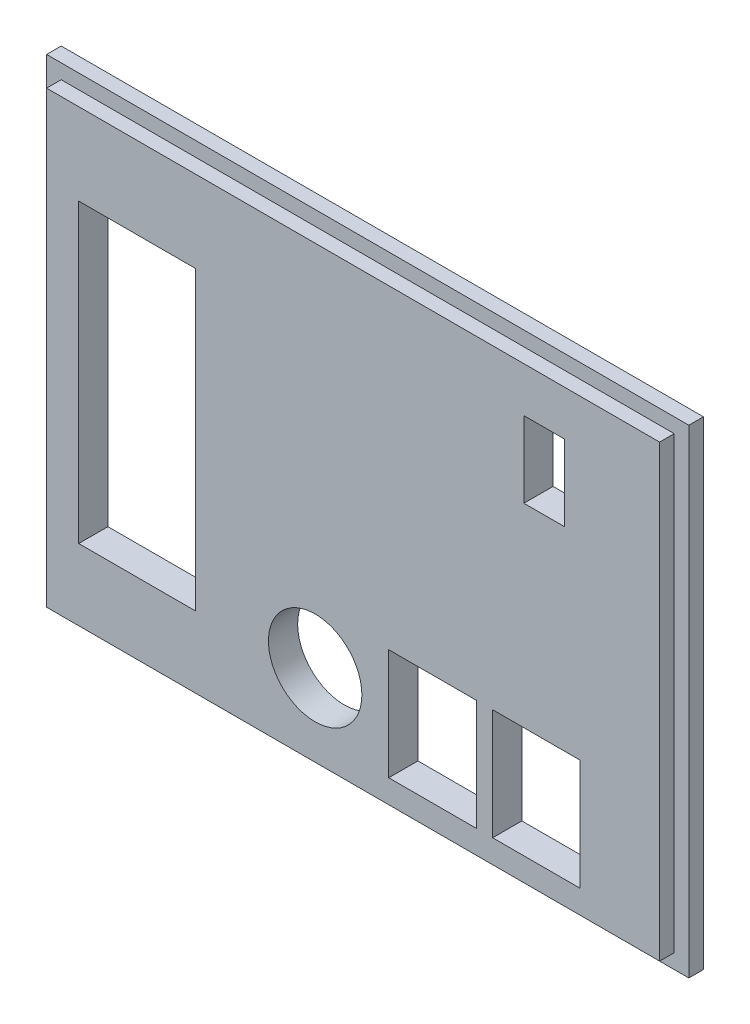
SolidWorks part; units mm, degrees
ref_plane "Front" through (0, 0, 0) normal (0, 0, 1) x (1, 0, 0)
ref_plane "Top" through (0, 0, 0) normal (0, 1, 0) x (1, 0, 0)
ref_plane "Right" through (0, 0, 0) normal (1, 0, 0) x (0, 0, -1)
sketch "Sketch2" plane through (0, 0, 0) normal (0, 0, 1) x (1, 0, 0)
  line L1 (55, 41) -> (-55, 41)
  line L2 (55, 41) -> (55, -41)
  line L3 (55, -41) -> (-55, -41)
  line L4 (-55, 41) -> (-55, -41)
  line L5 (55, 41) -> (-55, -41) construction
  line L6 (55, -41) -> (-55, 41) construction
  point P0 (0, 0)
extrude "Boss-Extrude1" add sketch "Sketch2" along normal blind 5
sketch "Sketch3" plane through (0, 0, 5) normal (0, 0, 1) x (1, 0, 0)
  line L0 (-55, 41) -> (55, 41)
  line L1 (55, 41) -> (55, 38.5)
  line L2 (55, -41) -> (55, 41) construction
  line L3 (55, 38.5) -> (-55, 38.5)
  line L4 (-55, 41) -> (-55, -41) construction
  line L5 (-55, 38.5) -> (-55, 41)
  line L6 (-55, 38.5) -> (-55, -41)
  line L15 (55, 38.5) -> (55, -38.4735)
  line M9 (-55, 41) -> (-55, -41)
  line M11 (55, -41) -> (55, 41)
  line M12 (55, 41) -> (-55, 41)
  dimension "D1" = 2.5
extrude "Cut-Extrude1" [suppressed] cut sketch "Sketch3" against normal blind 2.5 contours L3 M11 M12 M9
sketch "Sketch4" [suppressed] plane through (0, 0, 5) normal (0, 0, 1) x (1, 0, 0)
  line L0 (-55, 38.5) -> (-55, -41)
  line L1 (-55, -41) -> (-52.5, -41)
  line L2 (-55, -41) -> (55, -41) construction
  line L3 (-52.5, -41) -> (-52.5, 38.5)
  line L4 (55, 38.5) -> (-55, 38.5) construction
  line L5 (-52.5, 38.5) -> (-55, 38.5)
  dimension "D1" = 2.5
extrude "Cut-Extrude2" [suppressed] cut sketch "Sketch4" against normal blind 2.5
sketch "Sketch5" [suppressed] plane through (0, 0, 5) normal (0, 0, 1) x (1, 0, 0)
  line L0 (-52.5, -38.5) -> (55, -38.5)
  line L1 (-52.5, -41) -> (-52.5, 38.5) construction
  line L2 (55, -41) -> (55, 38.5) construction
  line L3 (55, -38.5) -> (55, -41)
  line L4 (55, -41) -> (-52.5, -41)
  line L5 (-52.5, -41) -> (-52.5, -38.5)
  dimension "D1" = 2.5
extrude "Cut-Extrude3" [suppressed] cut sketch "Sketch5" against normal blind 2.5
sketch "Sketch6" [suppressed] plane through (0, 0, 5) normal (0, 0, 1) x (1, 0, 0)
  line L0 (55, 38.5) -> (55, -38.5)
  line L1 (55, -38.5) -> (52.5, -38.5)
  line L2 (55, -38.5) -> (-52.5, -38.5) construction
  line L3 (52.5, -38.5) -> (52.5, 38.5)
  line L4 (55, 38.5) -> (-52.5, 38.5) construction
  line L5 (52.5, 38.5) -> (55, 38.5)
  dimension "D1" = 2.5
extrude "Cut-Extrude4" [suppressed] cut sketch "Sketch6" against normal blind 2.5
sketch "Sketch7" plane through (0, 0, 0) normal (0, 0, -1) x (-1, 0, 0)
  line L0 (-55, 41) -> (-55, 38)
  line L1 (-55, -41) -> (-55, 41) construction
  line L2 (-55, 38) -> (-52, 38)
  line L3 (-52, 38) -> (-52, -38)
  line L4 (-52, -38) -> (52, -38)
  line L5 (52, -38) -> (52, 38)
  line L6 (52, 38) -> (51.9896, 37.9992)
  line L7 (-52, 38) -> (51.9896, 37.9992)
  dimension "D1" = 3
  dimension "D2" = 3
  dimension "D3" = 76
  dimension "D4" = 104
extrude "Cut-Extrude5" [suppressed] cut sketch "Sketch7" against normal blind 3 contours L7 L6 L5 L4 L3
sketch "Sketch8" [suppressed] plane through (0, 0, 5) normal (0, 0, 1) x (1, 0, 0)
  line L0 (52.5, -30.8) -> (36.25, -30.8)
  line L1 (52.5, 38.5) -> (52.5, -38.5) construction
  line L2 (36.25, -30.8) -> (36.25, -38.5)
  line L3 (52.5, -38.5) -> (-52.5, -38.5) construction
  line L4 (36.25, -30.8) -> (29.25, -30.8)
  line L5 (29.25, -30.8) -> (29.25, -17.8)
  line L6 (29.25, -17.8) -> (36.25, -17.8)
  line L7 (36.25, -17.8) -> (36.25, -30.8)
  dimension "D1" = 16.25
  dimension "D2" = 7.7
  dimension "D3" = 13
  dimension "D4" = 7
extrude "Cut-Extrude6" [suppressed] cut sketch "Sketch8" against normal blind 5 contours L4 L5 L6 L7
sketch "Sketch9" [suppressed] plane through (0, 0, 5) normal (0, 0, 1) x (1, 0, 0)
  line L0 (-9.3, 38.5) -> (-9.3, 27.65)
  line L1 (52.5, 38.5) -> (-52.5, 38.5) construction
  line L2 (-9.3, 27.65) -> (-52.5, 27.65)
  line L3 (-52.5, -38.5) -> (-52.5, 38.5) construction
  circle A0 centre (-9.3, 27.65) radius 6.5
  dimension "D1" = 43.2
  dimension "D2" = 10.85
extrude "Cut-Extrude7" [suppressed] cut sketch "Sketch9" against normal blind 5 contours A0
sketch "Sketch10" [suppressed] plane through (0, 0, 5) normal (0, 0, 1) x (1, 0, 0)
  line L0 (13.6, 38.5) -> (13.6, 25)
  line L1 (52.5, 38.5) -> (-52.5, 38.5) construction
  line L2 (13.6, 25) -> (52.5, 25)
  line L3 (52.5, 38.5) -> (52.5, -38.5) construction
  line L5 (6.1, 34.5) -> (21.1, 34.5)
  line L6 (6.1, 34.5) -> (6.1, 15.5)
  line L7 (6.1, 15.5) -> (21.1, 15.5)
  line L8 (21.1, 34.5) -> (21.1, 15.5)
  line L9 (6.1, 34.5) -> (21.1, 15.5) construction
  line L10 (6.1, 15.5) -> (21.1, 34.5) construction
  dimension "D1" = 13.5
  dimension "D2" = 38.9
  dimension "D3" = 19
  dimension "D4" = 15
extrude "Cut-Extrude10" [suppressed] cut sketch "Sketch10" against normal blind 5 contours L8 L2 L0 L5 L6 L7 | L8 L5 L0 L2
sketch "Sketch12" [suppressed] plane through (0, 0, 5) normal (0, 0, 1) x (1, 0, 0)
  line L0 (31.4, 38.5) -> (31.4, 25)
  line L1 (52.5, 38.5) -> (-52.5, 38.5) construction
  line L2 (31.4, 25) -> (52.5, 25)
  line L3 (52.5, 38.5) -> (52.5, -38.5) construction
  line L5 (23.9, 34.5) -> (38.9, 34.5)
  line L6 (23.9, 34.5) -> (23.9, 15.5)
  line L7 (23.9, 15.5) -> (38.9, 15.5)
  line L8 (38.9, 34.5) -> (38.9, 15.5)
  line L9 (23.9, 34.5) -> (38.9, 15.5) construction
  line L10 (23.9, 15.5) -> (38.9, 34.5) construction
  dimension "D1" = 13.5
  dimension "D2" = 21.1
  dimension "D3" = 19
  dimension "D4" = 15
extrude "Cut-Extrude11" [suppressed] cut sketch "Sketch12" against normal blind 5 contours L8 L2 L0 L5 L6 L7 | L8 L5 L0 L2
sketch "Sketch13" plane through (0, 0, 5) normal (0, 0, 1) x (1, 0, 0)
  line L4 (-47, 24.5) -> (-47, -26.3)
  line L5 (-47, -26.3) -> (-47, 24.5)
  line L6 (-47, -26.3) -> (-26.9729, -26.3)
  line L7 (-26.9729, -26.3) -> (-26.9729, 24.5)
  line L8 (-26.9729, 24.5) -> (-47, 24.5)
extrude "Cut-Extrude12" cut sketch "Sketch13" against normal blind 5 contours L7 L8 L4 L6
sketch "Sketch14" plane through (0, 0, 5) normal (0, 0, 1) x (1, 0, 0)
  line L0 (-55, 41) -> (-52.5016, 41)
  line L1 (55, 41) -> (-55, 41) construction
  line L2 (-52.5016, 41) -> (-52.5016, -41)
  line L3 (-55, -41) -> (55, -41) construction
  line L4 (-52.5016, -41) -> (-55, -41)
  line L5 (-55, -41) -> (-55, 41)
extrude "Cut-Extrude13" cut sketch "Sketch14" against normal blind 2.5
sketch "Sketch15" plane through (0, 0, 5) normal (0, 0, 1) x (1, 0, 0)
  line L0 (-52.5016, -41) -> (-52.5016, -38.4999)
  line L1 (-52.5016, -41) -> (-52.5016, 41) construction
  line L2 (-52.5016, -38.4999) -> (55, -38.4999)
  line L3 (55, -41) -> (55, 41) construction
  line L4 (55, -38.4999) -> (55, -41)
  line L5 (55, -41) -> (-52.5016, -41)
extrude "Cut-Extrude14" cut sketch "Sketch15" against normal blind 2.5
sketch "Sketch16" plane through (0, 0, 5) normal (0, 0, 1) x (1, 0, 0)
  line L0 (-52.5016, 41) -> (-52.5016, 38.4983)
  line L1 (-52.5016, -38.4999) -> (-52.5016, 41) construction
  line L2 (-52.5016, 38.4983) -> (55, 38.4983)
  line L3 (55, -38.4999) -> (55, 41) construction
  line L4 (55, 38.4983) -> (55, 41)
  line L5 (55, 41) -> (-52.5016, 41)
extrude "Cut-Extrude15" cut sketch "Sketch16" against normal blind 2.5
sketch "Sketch18" plane through (0, 0, 5) normal (0, 0, 1) x (1, 0, 0)
  line L0 (55, 38.4983) -> (52.5, 38.4983)
  line L1 (-52.5016, 38.4983) -> (55, 38.4983) construction
  line L2 (52.5, 38.4983) -> (52.5, -38.4999)
  line L3 (55, -38.4999) -> (-52.5016, -38.4999) construction
  line L4 (52.5, -38.4999) -> (55, -38.4999)
  line L5 (55, -38.4999) -> (55, 38.4983)
  dimension "D1" = 2.5
extrude "Cut-Extrude18" cut sketch "Sketch18" against normal blind 2.5
sketch "Sketch19" plane through (0, 0, 5) normal (0, 0, 1) x (1, 0, 0)
  line L0 (13.6, -38.4999) -> (13.6, -24.9999)
  line L1 (52.5, -38.4999) -> (-52.5016, -38.4999) construction
  line L2 (13.6, -24.9999) -> (52.5, -24.9999)
  line L3 (52.5, 38.4983) -> (52.5, -38.4999) construction
  line L5 (6.1, -15.4999) -> (21.1, -15.4999)
  line L6 (6.1, -15.4999) -> (6.1, -34.4999)
  line L7 (6.1, -34.4999) -> (21.1, -34.4999)
  line L8 (21.1, -15.4999) -> (21.1, -34.4999)
  line L9 (6.1, -15.4999) -> (21.1, -34.4999) construction
  line L10 (6.1, -34.4999) -> (21.1, -15.4999) construction
  dimension "D1" = 38.9
  dimension "D2" = 13.5
  dimension "D3" = 19
  dimension "D4" = 15
extrude "Cut-Extrude19" cut sketch "Sketch19" against normal blind 10 contours L8 L5 L6 L7 L0 L2 | L8 L2 L0 L7
sketch "Sketch20" plane through (0, 0, 5) normal (0, 0, 1) x (1, 0, 0)
  line L0 (52.5, -24.9999) -> (31.4, -24.9999)
  line L1 (52.5, 38.4983) -> (52.5, -38.4999) construction
  line L2 (31.4, -24.9999) -> (31.4, -38.4999)
  line L3 (52.5, -38.4999) -> (-52.5016, -38.4999) construction
  line L5 (23.9, -15.4999) -> (38.9, -15.4999)
  line L6 (23.9, -15.4999) -> (23.9, -34.4999)
  line L7 (23.9, -34.4999) -> (38.9, -34.4999)
  line L8 (38.9, -15.4999) -> (38.9, -34.4999)
  line L9 (23.9, -15.4999) -> (38.9, -34.4999) construction
  line L10 (23.9, -34.4999) -> (38.9, -15.4999) construction
  dimension "D1" = 21.1
  dimension "D2" = 13.5
  dimension "D3" = 19
  dimension "D4" = 15
extrude "Cut-Extrude20" cut sketch "Sketch20" against normal blind 10 contours L8 L5 L6 L7 L2 L0 | L8 L0 L2 L7
sketch "Sketch21" plane through (0, 0, 5) normal (0, 0, 1) x (1, 0, 0)
  line L0 (-52.5016, -24.4999) -> (-6.5016, -24.4999)
  line L1 (-52.5016, -38.4999) -> (-52.5016, 38.4983) construction
  line L2 (-6.5016, -24.4999) -> (-6.5016, -38.4999)
  line L3 (52.5, -38.4999) -> (-52.5016, -38.4999) construction
  circle A0 centre (-6.5016, -24.4999) radius 8
  dimension "D1" = 46
  dimension "D2" = 14
extrude "Cut-Extrude21" cut sketch "Sketch21" against normal blind 8 contours L2 A0 L0 | L0 A0 L2
sketch "Sketch22" plane through (0, 0, 5) normal (0, 0, 1) x (1, 0, 0)
  line L0 (52.5, 30.7983) -> (36.25, 30.7983)
  line L1 (52.5, 38.4983) -> (52.5, -38.4999) construction
  line L2 (36.25, 30.7983) -> (36.25, 38.4983)
  line L3 (-52.5016, 38.4983) -> (52.5, 38.4983) construction
  line L4 (36.25, 30.7983) -> (36.25, 17.7983)
  line L5 (36.25, 17.7983) -> (29.25, 17.7983)
  line L6 (29.25, 17.7983) -> (29.25, 30.7983)
  line L7 (29.25, 30.7983) -> (36.25, 30.7983)
  dimension "D1" = 7.7
  dimension "D2" = 16.25
  dimension "D3" = 13
  dimension "D4" = 7
extrude "Cut-Extrude22" cut sketch "Sketch22" against normal blind 10 contours L7 L6 L5 L4
